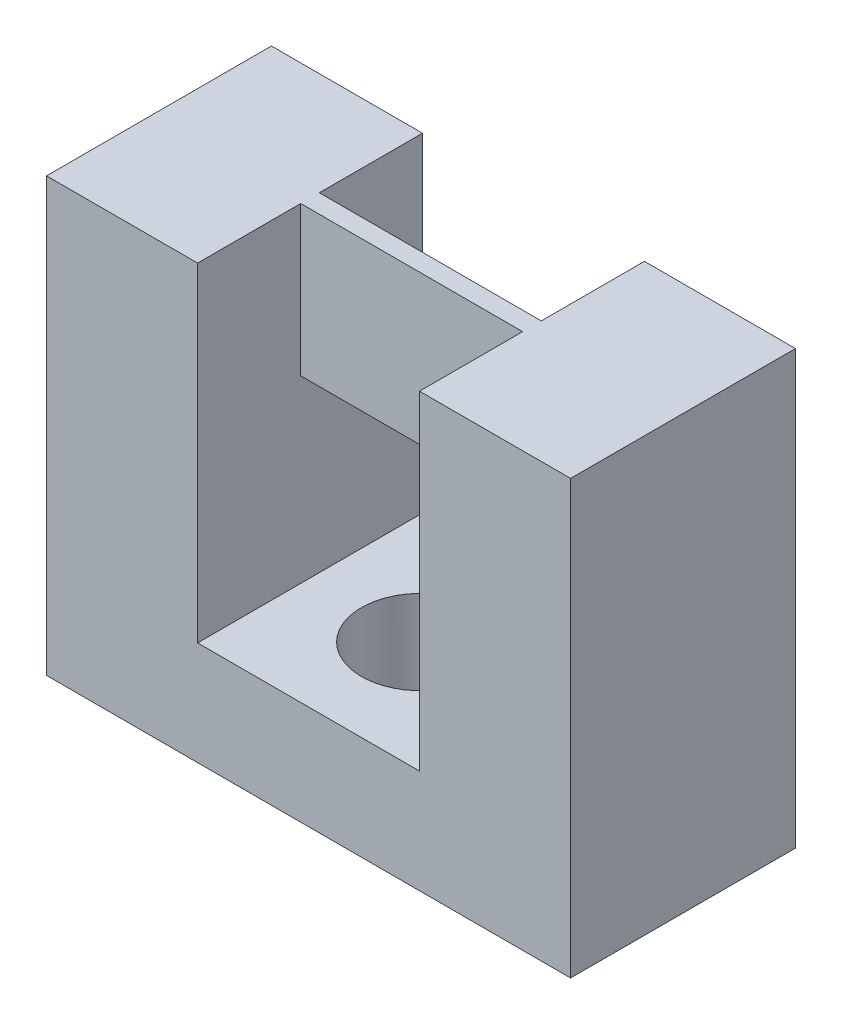
SolidWorks part; units mm, degrees
ref_plane "Front Plane" through (0, 0, 0) normal (0, 0, 1) x (1, 0, 0)
ref_plane "Top Plane" through (0, 0, 0) normal (0, 1, 0) x (1, 0, 0)
ref_plane "Right Plane" through (0, 0, 0) normal (1, 0, 0) x (0, 0, -1)
sketch "Sketch1" plane through (0, 0, 0) normal (0, 0, 1) x (1, 0, 0)
  line L1 (-7.025, -5.8) -> (7.025, -5.8)
  line L2 (-7.025, -5.8) -> (-7.025, 5.8)
  line L3 (-7.025, 5.8) -> (7.025, 5.8)
  line L4 (7.025, -5.8) -> (7.025, 5.8)
  line L5 (-7.025, -5.8) -> (7.025, 5.8) construction
  line L6 (-7.025, 5.8) -> (7.025, -5.8) construction
  point P0 (0, 0)
  dimension "D1" = 14.05
  dimension "D2" = 11.6
extrude "Boss-Extrude1" add sketch "Sketch1" along normal blind 6.03
sketch "Sketch2" plane through (0, 0, 6.03) normal (0, 0, 1) x (1, 0, 0)
  line L0 (2.975, 5.8) -> (2.975, -3.02)
  line L1 (7.025, 5.8) -> (-7.025, 5.8) construction
  line L2 (2.975, -3.02) -> (-2.975, -3.02)
  line L3 (-2.975, -3.02) -> (-2.975, 5.8)
  line L4 (7.025, -5.8) -> (7.025, 5.8) construction
  line L5 (-7.025, 5.8) -> (-7.025, -5.8) construction
  line L6 (-7.025, -5.8) -> (7.025, -5.8) construction
  line L7 (-2.975, 5.8) -> (2.975, 5.8)
  dimension "D1" = 4.05
  dimension "D2" = 4.05
  dimension "D3" = 2.78
extrude "Cut-Extrude2" cut sketch "Sketch2" against normal blind 6.03
sketch "Sketch3" plane through (-2.975, 0, 0) normal (1, 0, 0) x (0, 0, -1)
  line L0 (0, 5.8) -> (-6.03, 5.8) construction
  line L1 (-3.265, 5.8) -> (-2.765, 5.8)
  line L2 (-3.265, 5.8) -> (-3.265, 1.8)
  line L3 (-3.265, 1.8) -> (-2.765, 1.8)
  line L4 (-2.765, 5.8) -> (-2.765, 1.8)
  point P6 (-3.015, 5.8)
  point P7 (-3.015, 5.8)
  dimension "D1" = 0.5
  dimension "D2" = 4
  dimension "D3" = 0
extrude "Boss-Extrude2" add sketch "Sketch3" along normal blind 6.03
hole_wizard "M3 Clearance Hole1" positions "Sketch4" profile "Sketch5" hole size "M3" standard "ANSI Metric" end condition up to next
sketch "Sketch4" plane through (0, -5.8, 0) normal (0, -1, 0) x (-1, 0, 0)
  point P0 (0, -3.015)
sketch "Sketch5" plane through (0, -5.8, 3.015) normal (1, 0, 0) x (0, 0, -1)
  line L0 (0, 0) -> (0, 2.78)
  line L1 (0, 2.78) -> (1.6, 2.78)
  line L2 (1.6, 2.78) -> (1.6, 0)
  line L5 (1.6, 0) -> (0, 0)
  line L11 (0, -6.35) -> (0, 107.95) construction
  dimension "Thru Hole Dia." = 3.2
  dimension "Thru Hole Depth" = 2.78
